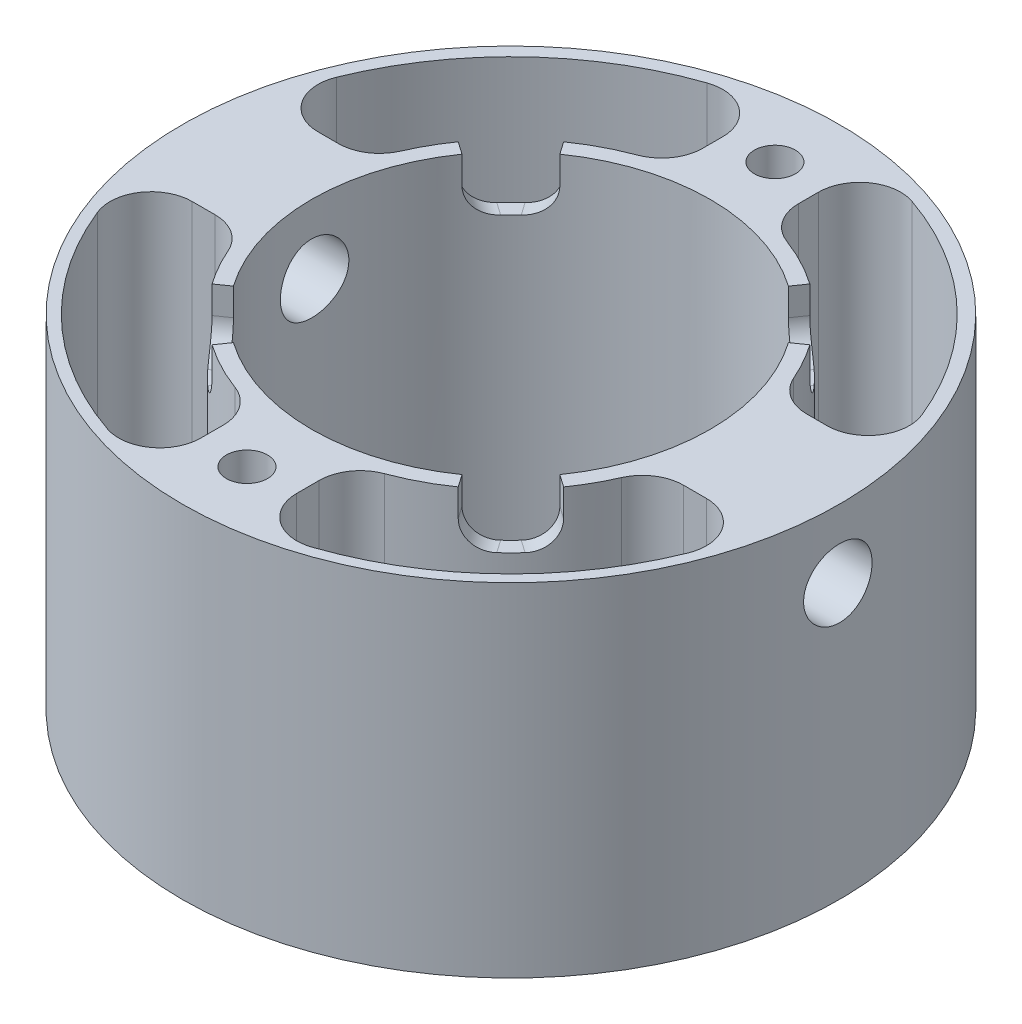
SolidWorks part; units mm, degrees
material "1060 Alloy"
ref_plane "Front Plane" through (0, 0, 0) normal (0, 0, 1) x (1, 0, 0)
ref_plane "Top Plane" through (0, 0, 0) normal (0, 1, 0) x (1, 0, 0)
ref_plane "Right Plane" through (0, 0, 0) normal (1, 0, 0) x (0, 0, -1)
sketch "Sketch3" plane through (0, 0, 0) normal (0, 1, 0) x (1, 0, 0)
  circle A0 centre (0, 0) radius 24
  circle A1 centre (0, 0) radius 14.55
  dimension "D1" = 48
  dimension "D2" = 29.1
extrude "Boss-Extrude1" add sketch "Sketch3" along normal blind 10 and the other way blind 15
sketch "Sketch4" plane through (0, 0, 0) normal (1, 0, 0) x (0, 0, -1)
  circle A0 centre (0, 5) radius 2.5
  dimension "D1" = 5
  dimension "D2" = 5
extrude "Cut-Extrude2" cut sketch "Sketch4" against normal blind 100 from offset 50
sketch "Sketch5" plane through (0, 10, 0) normal (0, 1, 0) x (1, 0, 0)
  circle A0 centre (0, 19.275) radius 1.5
  circle A3 centre (0, -19.275) radius 1.5
  dimension "D1" = 3
  dimension "D4" = 3
  dimension "D2" = 19.275
  dimension "D3" = 19.275
extrude "Cut-Extrude3" cut sketch "Sketch5" against normal blind 100
sketch "Sketch7" plane through (0, 10, 0) normal (0, 1, 0) x (1, 0, 0)
  line L0 (3.5, 15.275) -> (3.5, 22.775)
  line L1 (15.0109, 4.5) -> (22.5987, 4.5)
  arc A0 (3.5, 22.775) -> (22.5987, 4.5) centre (0, 0) cw
  arc A1 (3.5, 15.275) -> (15.0109, 4.5) centre (0, 0) cw
  dimension "D1" = 3.5
  dimension "D2" = 22.775
  dimension "D4" = 4.5
  dimension "D3" = 3.5
  dimension "D5" = 15.275
  dimension "D6" = 4.5
extrude "Cut-Extrude6" cut sketch "Sketch7" against normal blind 26
sketch "Sketch9" plane through (0, 10, 0) normal (0, 1, 0) x (1, 0, 0)
  line L0 (15.0109, -4.5) -> (22.775, -4.5)
  line L1 (3.5, -15.275) -> (3.5, -22.95)
  arc A0 (15.0109, -4.5) -> (3.5, -15.275) centre (0, 0) cw
  arc A1 (22.775, -4.5) -> (3.5, -22.95) centre (0, 0) cw
  dimension "D2" = 4.5
  dimension "D3" = 4.5
  dimension "D4" = 22.775
  dimension "D5" = 3.5
  dimension "D6" = 3.5
  dimension "D1" = 15.275
extrude "Cut-Extrude7" cut sketch "Sketch9" against normal blind 26
sketch "Sketch10" plane through (0, 10, 0) normal (0, 1, 0) x (1, 0, 0)
  line L0 (-3.5, 15.275) -> (-3.5, 22.775)
  line L1 (-22.5987, 4.5) -> (-15.0109, 4.5)
  arc A0 (-3.5, 15.275) -> (-15.0109, 4.5) centre (0, 0) ccw
  arc A1 (-3.5, 22.775) -> (-22.5987, 4.5) centre (0, 0) ccw
  dimension "D1" = 3.5
  dimension "D6" = 4.5
  dimension "D3" = 4.5
  dimension "D2" = 15.275
  dimension "D4" = 3.5
  dimension "D5" = 22.775
extrude "Cut-Extrude8" cut sketch "Sketch10" against normal blind 26
sketch "Sketch11" plane through (0, 10, 0) normal (0, 1, 0) x (1, 0, 0)
  line L0 (-15.0109, -4.5) -> (-22.775, -4.5)
  line L1 (-3.5, -15.275) -> (-3.5, -22.95)
  arc A0 (-22.775, -4.5) -> (-3.5, -22.95) centre (0, 0) ccw
  arc A1 (-3.5, -15.275) -> (-15.0109, -4.5) centre (0, 0) cw
  dimension "D4" = 4.5
  dimension "D3" = 3.5
  dimension "D2" = 4.5
  dimension "D5" = 3.5
  dimension "D1" = 22.775
  dimension "D6" = 15.275
extrude "Cut-Extrude9" cut sketch "Sketch11" against normal blind 26
fillet "Fillet5" radius 3 16 edges at (3.5, -2.5, -15.275) (3.5, -2.5, -22.775) (15.0109, -2.5, -4.5) (22.5987, -2.5, -4.5) (15.0109, -2.5, 4.5) (22.775, -2.5, 4.5) (3.5, -2.5, 15.275) (3.5, -2.5, 22.95) (-3.5, -2.5, 22.95) (-3.5, -2.5, 15.275) (-22.775, -2.5, 4.5) (-15.0109, -2.5, 4.5) (-15.0109, -2.5, -4.5) (-22.5987, -2.5, -4.5) (-3.5, -2.5, -15.275) (-3.5, -2.5, -22.775)
sketch "Sketch19" plane through (0, 10, 0) normal (0, 1, 0) x (1, 0, 0)
  line L0 (0, 0) -> (-15.6709, 0)
  line L1 (0, 0) -> (0, 15.6709)
  line L2 (0, 0) -> (15.6709, 0)
  line L3 (0, 0) -> (0, -15.6709)
  line L4 (0, 0) -> (-12.8368, 8.9884)
  line L5 (0, 0) -> (-8.9884, 12.8368)
  line L6 (0, 0) -> (8.9884, 12.8368)
  line L7 (0, 0) -> (12.8368, 8.9884)
  line L8 (0, 0) -> (-8.9884, -12.8368)
  line L9 (0, 0) -> (-12.8368, -8.9884)
  line L10 (0, 0) -> (8.9884, -12.8368)
  line L11 (0, 0) -> (12.8368, -8.9884)
  circle A0 centre (0, 0) radius 14.55
  circle A1 centre (0, 0) radius 15.6709
  arc M19 (-14.3509, -6.2949) -> (-5.4556, -14.6905) centre (0, 0) ccw
  arc M23 (-5.4556, 14.6905) -> (-14.3509, 6.2949) centre (0, 0) ccw
  arc M31 (5.4556, -14.6905) -> (14.3509, -6.2949) centre (0, 0) ccw
  arc M43 (14.3509, 6.2949) -> (5.4556, 14.6905) centre (0, 0) ccw
  circle M50 centre (0, 0) radius 14.55
  dimension "D1" = 35
  dimension "D2" = 20
  dimension "D3" = 35
  dimension "D4" = 20
  dimension "D5" = 35
  dimension "D6" = 20
  dimension "D7" = 35
  dimension "D8" = 20
extrude "Cut-Extrude12" cut sketch "Sketch19" against normal blind 4 contours L5 L4 M50 M23 | L7 L6 M50 M43 | L11 L10 M50 M31 | L9 L8 M50 M19
fillet "Fillet10" radius 2 8 edges at (-12.3777, 6, 8.667) (-8.667, 6, 12.3777) (8.667, 6, 12.3777) (12.3777, 6, 8.667) (12.3777, 6, -8.667) (8.667, 6, -12.3777) (-12.3777, 6, -8.667) (-8.667, 6, -12.3777)
sketch "Sketch20" plane through (0, -15, 0) normal (0, -1, 0) x (1, 0, 0)
  circle A0 centre (-19.275, 0) radius 2.5
  circle A1 centre (19.275, 0) radius 2.5
  dimension "D2" = 19.275
  dimension "D3" = 5
  dimension "D4" = 5
  dimension "D1" = 19.275
extrude "Cut-Extrude13" cut sketch "Sketch20" against normal blind 15
equation "\"TubeInnerDiameter\"= 48mm"
equation "\"MotorCasingDiameter\"= 29.1mm"
equation "\"BoltDiameter\"= 5mm"
equation "\"SpacerHeight\"= 10mm"
equation "\"D1@Sketch3\"=\"TubeInnerDiameter\""
equation "\"D1@Boss-Extrude1\"=\"SpacerHeight\""
equation "\"D1@Sketch4\"=\"BoltDiameter\""
equation "\"D2@Sketch4\"=\"SpacerHeight\"/2"
equation "\"TopBoltDiameter\"= 3mm"
equation "\"D1@Sketch5\"=\"TopBoltDiameter\""
equation "\"D2@Sketch5\"=(\"TubeInnerDiameter\"/2-\"MotorCasingDiameter\"/2)/2+\"MotorCasingDiameter\"/2"
equation "\"D4@Sketch5\"=\"TopBoltDiameter\""
equation "\"D3@Sketch5\"=(\"TubeInnerDiameter\"/2-\"MotorCasingDiameter\"/2)/2+\"MotorCasingDiameter\"/2"
equation "\"PressureChannelWidth\"= 8mm"
equation "\"IgniterChannelDiameter\"= 2.8mm"
equation "\"D1@Sketch7\"=\"TopBoltDiameter\"/2+\"BoltChannelSeparation\""
equation "\"D4@Sketch7\"=\"BoltDiameter\"/2+\"BoltChannelSeparation\""
equation "\"BoltChannelSeparation\"= 2mm"
equation "\"D3@Sketch7\"=\"TopBoltDiameter\"/2+\"BoltChannelSeparation\""
equation "\"D5@Sketch7\"=(\"TubeInnerDiameter\"/2+\"MotorCasingDiameter\"/2)/2-\"PressureChannelWidth\"/2"
equation "\"D6@Sketch7\"=\"BoltDiameter\"/2+\"BoltChannelSeparation\""
equation "\"D2@Sketch7\"=(\"TubeInnerDiameter\"/2+\"MotorCasingDiameter\"/2)/2+\"PressureChannelWidth\"/2-0.5"
equation "\"D2@Sketch3\"=\"MotorCasingDiameter\""
equation "\"ChamferRadius\"= 3mm"
equation "\"D2@Sketch9\"=\"BoltDiameter\"/2+\"BoltChannelSeparation\""
equation "\"D3@Sketch9\"=\"BoltDiameter\"/2+\"BoltChannelSeparation\""
equation "\"D4@Sketch9\"=(\"TubeInnerDiameter\"/2+\"MotorCasingDiameter\"/2)/2+\"PressureChannelWidth\"/2-0.5mm"
equation "\"D5@Sketch9\"=\"TopBoltDiameter\"/2+\"BoltChannelSeparation\""
equation "\"D6@Sketch9\"=\"TopBoltDiameter\"/2+\"BoltChannelSeparation\""
equation "\"D1@Sketch10\"=\"TopBoltDiameter\"/2+\"BoltChannelSeparation\""
equation "\"D2@Sketch10\"=(\"TubeInnerDiameter\"/2+\"MotorCasingDiameter\"/2)/2-\"PressureChannelWidth\"/2"
equation "\"D3@Sketch10\"=\"BoltDiameter\"/2+\"BoltChannelSeparation\""
equation "\"D4@Sketch10\"=\"TopBoltDiameter\"/2+\"BoltChannelSeparation\""
equation "\"D5@Sketch10\"=(\"TubeInnerDiameter\"/2+\"MotorCasingDiameter\"/2)/2+\"PressureChannelWidth\"/2-0.5mm"
equation "\"D6@Sketch10\"=\"BoltDiameter\"/2+\"BoltChannelSeparation\""
equation "\"D1@Sketch11\"=(\"TubeInnerDiameter\"/2+\"MotorCasingDiameter\"/2)/2+\"PressureChannelWidth\"/2-0.5mm"
equation "\"D2@Sketch11\"=\"BoltDiameter\"/2+\"BoltChannelSeparation\""
equation "\"D3@Sketch11\"=\"TopBoltDiameter\"/2+\"BoltChannelSeparation\""
equation "\"D4@Sketch11\"=\"BoltDiameter\"/2+\"BoltChannelSeparation\""
equation "\"D5@Sketch11\"=\"TopBoltDiameter\"/2+\"BoltChannelSeparation\""
equation "\"D6@Sketch11\"=(\"TubeInnerDiameter\"/2+\"MotorCasingDiameter\"/2)/2-\"PressureChannelWidth\"/2"
equation "\"D1@Fillet5\"=\"ChamferRadius\""
equation "\"D1@Sketch9\"=(\"TubeInnerDiameter\"/2+\"MotorCasingDiameter\"/2)/2-\"PressureChannelWidth\"/2"
equation "\"TopChannelDepth\"= 4mm"
equation "\"TopChannelChamferRadius\"= 2mm"
equation "\"HeightExtension\"= 15mm"
equation "\"D1@Cut-Extrude12\"=\"TopChannelDepth\""
equation "\"D1@Fillet10\"=\"TopChannelChamferRadius\""
equation "\"D2@Boss-Extrude1\"=\"HeightExtension\""
equation "\"D1@Sketch20\"=(\"TubeInnerDiameter\"/2+\"MotorCasingDiameter\"/2)/2"
equation "\"D2@Sketch20\"=(\"TubeInnerDiameter\"/2+\"MotorCasingDiameter\"/2)/2"
equation "\"D4@Sketch20\"=\"BoltDiameter\""
equation "\"D1@Cut-Extrude13\"=\"HeightExtension\""
